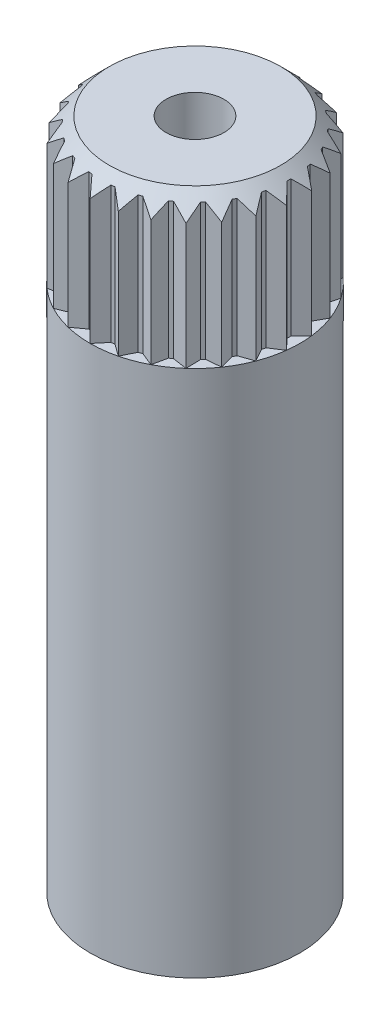
SolidWorks part; units mm, degrees
material "Polyethylene Cross-Linked"
ref_plane "Front Plane" through (0, 0, 0) normal (0, 0, 1) x (1, 0, 0)
ref_plane "Top Plane" through (0, 0, 0) normal (0, 1, 0) x (1, 0, 0)
ref_plane "Right Plane" through (0, 0, 0) normal (1, 0, 0) x (0, 0, -1)
sketch "ShaftS" plane through (0, 0, 0) normal (0, 1, 0) x (1, 0, 0)
  circle A0 centre (0, 0) radius 2.9
  dimension "D1" = 5.8
extrude "SHAFT" add sketch "ShaftS" along normal blind 14.6
sketch "ShaftExtensionS" plane through (0, 14.6, 0) normal (0, 1, 0) x (1, 0, 0)
  circle A0 centre (0, 0) radius 2.6
  circle A1 centre (0, 0) radius 2.9 construction
  dimension "D1" = 0.3
extrude "SHAFT EXTENSION" add sketch "ShaftExtensionS" along normal blind 4
sketch "ToothS" plane through (0, 18.6, 0) normal (0, 1, 0) x (1, 0, 0)
  line L0 (0, 2.6) -> (0, 2.9) construction
  line L1 (0, 2.9) -> (-0.2629, 2.5867)
  line L2 (0, 2.9) -> (0.2629, 2.5867)
  line L3 (-0.2629, 2.5867) -> (0.2629, 2.5867) construction
  arc A0 (0.2629, 2.5867) -> (-0.2629, 2.5867) centre (0, 0) ccw
  circle A3 centre (0, 0) radius 2.6 construction
  circle A4 centre (0, 0) radius 2.9 construction
  dimension "D1" = 80
  dimension "D2" = 0.5258
  dimension "D3" = 0.3
extrude "TOOTH" add sketch "ToothS" against normal up to body (18.6 mm away) separate body
pattern_circular "TOOTH CP" count 26 over 360 about axis through (0, 0, 0) along (0, 1, 0) of "TOOTH"
sketch "SmallBoreS" plane through (0, 18.6, 0) normal (0, 1, 0) x (1, 0, 0)
  circle A0 centre (0, 0) radius 0.8
  dimension "D1" = 1.6
extrude "SMALL BORE" cut sketch "SmallBoreS" against normal blind 4
sketch "TeethChamferS" plane through (0, 0, 0) normal (1, 0, 0) x (0, 0, -1)
  line L0 (2.9, 18.0697) -> (2.9, 18.6)
  line L1 (2.9, 18.6) -> (2.3697, 18.6)
  line L2 (2.3697, 18.6) -> (2.9, 18.0697)
  line L3 (2.9, 14.6) -> (2.9, 18.6) construction
  line L4 (2.9, 16.6) -> (0, 16.6) construction
  line L5 (0, 18.6) -> (0, 14.6) construction
  point P4 (2.9, 16.6)
  dimension "D1" = 45
  dimension "D2" = 0.75
revolve "TEETH CHAMFER" cut sketch "TeethChamferS" angle 360 about axis through (0, 18.6, 0) along (0, -1, 0)
